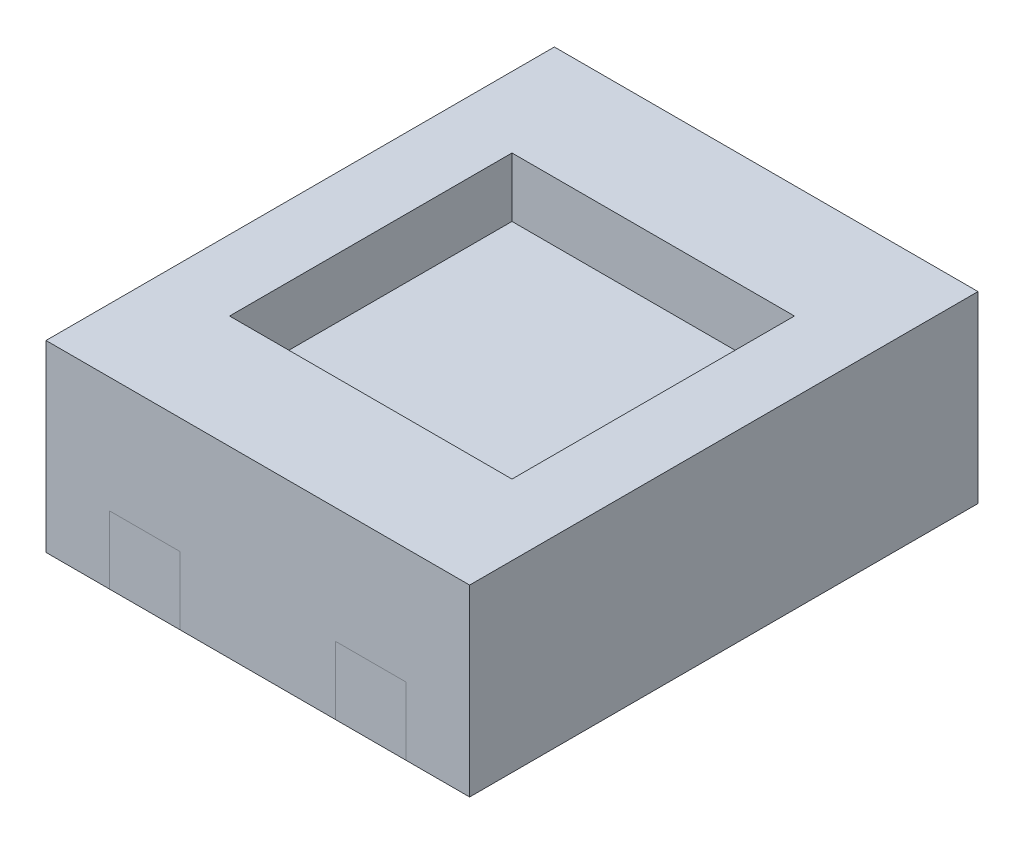
SolidWorks part; units mm, degrees
ref_plane "Front Plane" through (0, 0, 0) normal (0, 0, 1) x (1, 0, 0)
ref_plane "Top Plane" through (0, 0, 0) normal (0, 1, 0) x (1, 0, 0)
ref_plane "Right Plane" through (0, 0, 0) normal (1, 0, 0) x (0, 0, -1)
sketch "Sketch1" plane through (0, 0, 0) normal (0, 1, 0) x (1, 0, 0)
  line L0 (0.395, 0.52) -> (0.405, 0.52) construction
  line L1 (0.75, 0.9) -> (0.525, 0.9)
  line L2 (0.75, 0.9) -> (0.75, -0.9)
  line L3 (0.75, -0.9) -> (0.525, -0.9)
  line L4 (-0.75, 0.9) -> (-0.75, -0.9)
  line L5 (0.75, 0.9) -> (-0.75, -0.9) construction
  line L6 (0.75, -0.9) -> (-0.75, 0.9) construction
  line L8 (0.275, 0.9) -> (0.275, 0.52)
  line L9 (0.395, 0.4) -> (0.405, 0.4)
  line L10 (0.525, 0.9) -> (0.525, 0.52)
  line L11 (0.4, 0.52) -> (0.4, 0.5602) construction
  line L12 (0, 0.9) -> (0, -0.9) construction
  line L13 (-0.525, 0.9) -> (-0.525, 0.52)
  line L14 (-0.395, 0.4) -> (-0.405, 0.4)
  line L15 (-0.275, 0.9) -> (-0.275, 0.52)
  line L16 (-0.75, 0) -> (0.75, 0) construction
  line L17 (-0.395, -0.4) -> (-0.405, -0.4)
  line L18 (0.395, -0.4) -> (0.405, -0.4)
  line L19 (0.525, -0.9) -> (0.525, -0.52)
  line L20 (0.275, -0.9) -> (0.275, -0.52)
  line L21 (-0.275, -0.9) -> (-0.275, -0.52)
  line L22 (-0.525, -0.9) -> (-0.525, -0.52)
  line L23 (-0.525, 0.9) -> (-0.75, 0.9)
  line L24 (0.275, 0.9) -> (-0.275, 0.9)
  line L25 (-0.525, -0.9) -> (-0.75, -0.9)
  line L26 (0.275, -0.9) -> (-0.275, -0.9)
  arc A0 (0.405, 0.4) -> (0.525, 0.52) centre (0.405, 0.52) ccw
  arc A1 (0.395, 0.4) -> (0.275, 0.52) centre (0.395, 0.52) cw
  arc A2 (-0.405, 0.4) -> (-0.525, 0.52) centre (-0.405, 0.52) cw
  arc A3 (-0.395, 0.4) -> (-0.275, 0.52) centre (-0.395, 0.52) ccw
  arc A4 (0.405, -0.4) -> (0.525, -0.52) centre (0.405, -0.52) cw
  arc A5 (0.395, -0.4) -> (0.275, -0.52) centre (0.395, -0.52) ccw
  arc A6 (-0.395, -0.4) -> (-0.275, -0.52) centre (-0.395, -0.52) cw
  arc A7 (-0.405, -0.4) -> (-0.525, -0.52) centre (-0.405, -0.52) ccw
  point P0 (0, 0)
  point P12 (0.525, 0.4)
  dimension "D5" = 0.12
  dimension "D1" = 1.5
  dimension "D2" = 1.8
  dimension "D3" = 0.5
  dimension "D4" = 0.25
  dimension "D6" = 0.35
extrude "Boss-Extrude1" add sketch "Sketch1" along normal blind 0.24
sketch "Sketch2" plane through (0, 0.24, 0) normal (0, 1, 0) x (1, 0, 0)
  line L1 (0.5, -0.5) -> (-0.5, -0.5)
  line L2 (0.5, -0.5) -> (0.5, 0.5)
  line L3 (0.5, 0.5) -> (-0.5, 0.5)
  line L4 (-0.5, -0.5) -> (-0.5, 0.5)
  line L5 (0.5, -0.5) -> (-0.5, 0.5) construction
  line L6 (0.5, 0.5) -> (-0.5, -0.5) construction
  point P0 (0, 0)
  dimension "D1" = 1
extrude "Boss-Extrude2" add sketch "Sketch2" along normal blind 0.2 separate body
sketch "Sketch3" plane through (0, 0.24, 0) normal (0, 1, 0) x (1, 0, 0)
  line L1 (-0.75, 0.9) -> (0.75, 0.9)
  line L2 (-0.75, 0.9) -> (-0.75, -0.9)
  line L3 (-0.75, -0.9) -> (0.75, -0.9)
  line L4 (0.75, 0.9) -> (0.75, -0.9)
  line L5 (-0.5, 0.5) -> (0.5, 0.5)
  line L6 (-0.5, 0.5) -> (-0.5, -0.5)
  line L7 (-0.5, -0.5) -> (0.5, -0.5)
  line L8 (0.5, 0.5) -> (0.5, -0.5)
extrude "Boss-Extrude3" add sketch "Sketch3" along normal blind 0.2
sketch "Sketch4" plane through (0, 0.44, 0) normal (0, 1, 0) x (1, 0, 0)
  line L4 (-0.75, 0.9) -> (-0.75, -0.9)
  line L5 (-0.75, -0.9) -> (0.75, -0.9)
  line L6 (0.75, -0.9) -> (0.75, 0.9)
  line L7 (0.75, 0.9) -> (-0.75, 0.9)
  line L8 (-0.75, 0.9) -> (-0.75, -0.9)
  line L9 (-0.75, -0.9) -> (0.75, -0.9)
  line L10 (0.75, -0.9) -> (0.75, 0.9)
  line L11 (0.75, 0.9) -> (-0.75, 0.9)
  dimension "D1" = 0
extrude "Boss-Extrude4" add sketch "Sketch4" along normal blind 0.21
sketch "Sketch5" plane through (0, 0.24, 0) normal (0, -1, 0) x (1, 0, 0)
  line L0 (0.525, -0.9) -> (0.275, -0.9) construction
  line L1 (0.525, -0.9) -> (0.525, -0.52) construction
  line L2 (0.405, -0.4) -> (0.395, -0.4) construction
  line L3 (0.275, -0.52) -> (0.275, -0.9) construction
  line L4 (0.525, -0.9) -> (0.275, -0.9)
  line L5 (0.525, -0.9) -> (0.525, -0.52)
  line L6 (0.405, -0.4) -> (0.395, -0.4)
  line L7 (0.275, -0.52) -> (0.275, -0.9)
  line L8 (-0.395, -0.4) -> (-0.405, -0.4) construction
  line L9 (-0.275, -0.9) -> (-0.275, -0.52) construction
  line L10 (-0.275, -0.9) -> (-0.525, -0.9) construction
  line L11 (-0.525, -0.52) -> (-0.525, -0.9) construction
  line L12 (-0.395, -0.4) -> (-0.405, -0.4)
  line L13 (-0.275, -0.9) -> (-0.275, -0.52)
  line L14 (-0.275, -0.9) -> (-0.525, -0.9)
  line L15 (-0.525, -0.52) -> (-0.525, -0.9)
  line L16 (-0.525, 0.9) -> (-0.275, 0.9) construction
  line L17 (-0.275, 0.52) -> (-0.275, 0.9) construction
  line L18 (-0.405, 0.4) -> (-0.395, 0.4) construction
  line L19 (-0.525, 0.9) -> (-0.525, 0.52) construction
  line L20 (-0.525, 0.9) -> (-0.275, 0.9)
  line L21 (-0.275, 0.52) -> (-0.275, 0.9)
  line L22 (-0.405, 0.4) -> (-0.395, 0.4)
  line L23 (-0.525, 0.9) -> (-0.525, 0.52)
  line L24 (0.275, 0.9) -> (0.525, 0.9) construction
  line L25 (0.525, 0.52) -> (0.525, 0.9) construction
  line L26 (0.395, 0.4) -> (0.405, 0.4) construction
  line L27 (0.275, 0.9) -> (0.275, 0.52) construction
  line L28 (0.275, 0.9) -> (0.525, 0.9)
  line L29 (0.525, 0.52) -> (0.525, 0.9)
  line L30 (0.395, 0.4) -> (0.405, 0.4)
  line L31 (0.275, 0.9) -> (0.275, 0.52)
  arc A0 (0.525, -0.52) -> (0.405, -0.4) centre (0.405, -0.52) ccw construction
  arc A1 (0.395, -0.4) -> (0.275, -0.52) centre (0.395, -0.52) ccw construction
  arc A2 (0.525, -0.52) -> (0.405, -0.4) centre (0.405, -0.52) ccw
  arc A3 (0.395, -0.4) -> (0.275, -0.52) centre (0.395, -0.52) ccw
  arc A4 (-0.405, -0.4) -> (-0.525, -0.52) centre (-0.405, -0.52) ccw construction
  arc A5 (-0.275, -0.52) -> (-0.395, -0.4) centre (-0.395, -0.52) ccw construction
  arc A6 (-0.405, -0.4) -> (-0.525, -0.52) centre (-0.405, -0.52) ccw
  arc A7 (-0.275, -0.52) -> (-0.395, -0.4) centre (-0.395, -0.52) ccw
  arc A8 (-0.395, 0.4) -> (-0.275, 0.52) centre (-0.395, 0.52) ccw construction
  arc A9 (-0.525, 0.52) -> (-0.405, 0.4) centre (-0.405, 0.52) ccw construction
  arc A10 (-0.395, 0.4) -> (-0.275, 0.52) centre (-0.395, 0.52) ccw
  arc A11 (-0.525, 0.52) -> (-0.405, 0.4) centre (-0.405, 0.52) ccw
  arc A12 (0.405, 0.4) -> (0.525, 0.52) centre (0.405, 0.52) ccw construction
  arc A13 (0.275, 0.52) -> (0.395, 0.4) centre (0.395, 0.52) ccw construction
  arc A14 (0.405, 0.4) -> (0.525, 0.52) centre (0.405, 0.52) ccw
  arc A15 (0.275, 0.52) -> (0.395, 0.4) centre (0.395, 0.52) ccw
extrude "Boss-Extrude5" add sketch "Sketch5" along normal up to surface (0.24 mm away) separate body up to face at (0, 0, 0)
sketch "Sketch6" plane through (0, 0.65, 0) normal (0, 1, 0) x (1, 0, 0)
  line L4 (-0.5, -0.5) -> (0.5, -0.5)
  line L5 (-0.5, 0.5) -> (-0.5, -0.5)
  line L6 (0.5, 0.5) -> (-0.5, 0.5)
  line L7 (0.5, -0.5) -> (0.5, 0.5)
  line L8 (-0.5, -0.5) -> (0.5, -0.5)
  line L9 (-0.5, 0.5) -> (-0.5, -0.5)
  line L10 (0.5, 0.5) -> (-0.5, 0.5)
  line L11 (0.5, -0.5) -> (0.5, 0.5)
  dimension "D1" = 0
extrude "Cut-Extrude4" cut sketch "Sketch6" against normal up to surface (0.21 mm away) up to face at (0, 0.44, 0)
